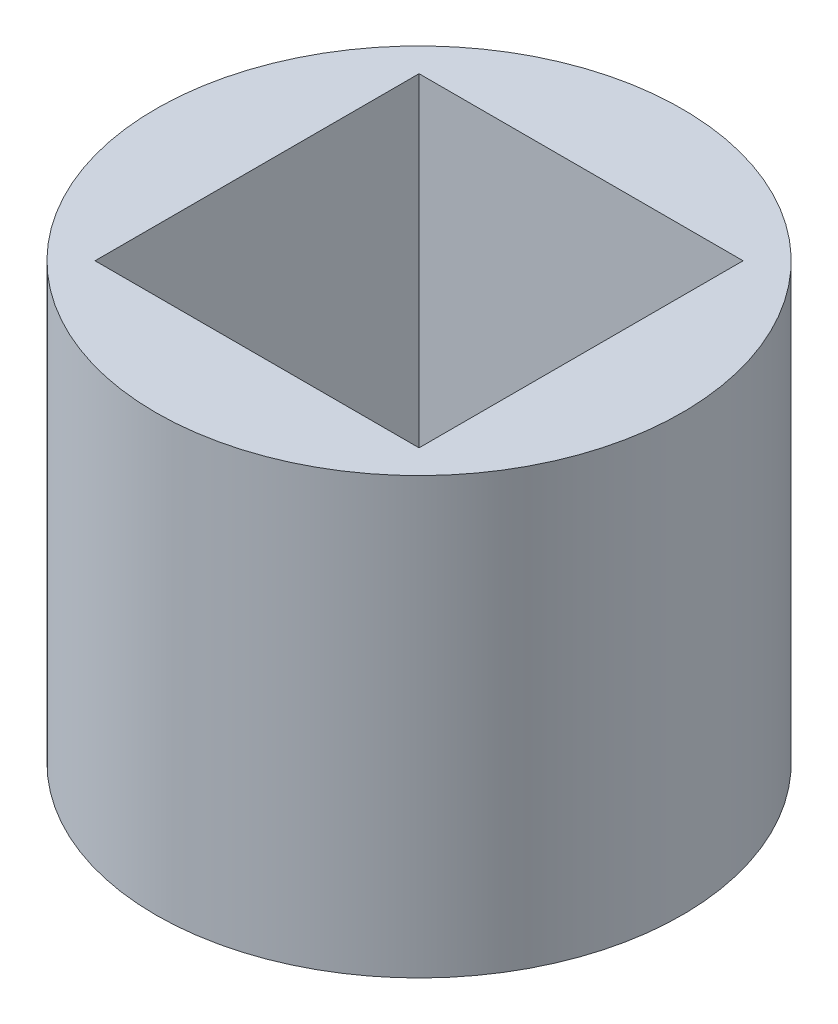
SolidWorks part; units mm, degrees
ref_plane "Front Plane" through (0, 0, 0) normal (0, 0, 1) x (1, 0, 0)
ref_plane "Top Plane" through (0, 0, 0) normal (0, 1, 0) x (1, 0, 0)
ref_plane "Right Plane" through (0, 0, 0) normal (1, 0, 0) x (0, 0, -1)
sketch "Sketch1" plane through (0, 0, 0) normal (0, 1, 0) x (1, 0, 0)
  line L1 (-7.82, 7.82) -> (7.82, 7.82)
  line L2 (-7.82, 7.82) -> (-7.82, -7.82)
  line L3 (-7.82, -7.82) -> (7.82, -7.82)
  line L4 (7.82, 7.82) -> (7.82, -7.82)
  line L5 (-7.82, 7.82) -> (7.82, -7.82) construction
  line L6 (-7.82, -7.82) -> (7.82, 7.82) construction
  circle A0 centre (0, 0) radius 12.7
extrude "Boss-Extrude1" add sketch "Sketch1" along normal blind 21
